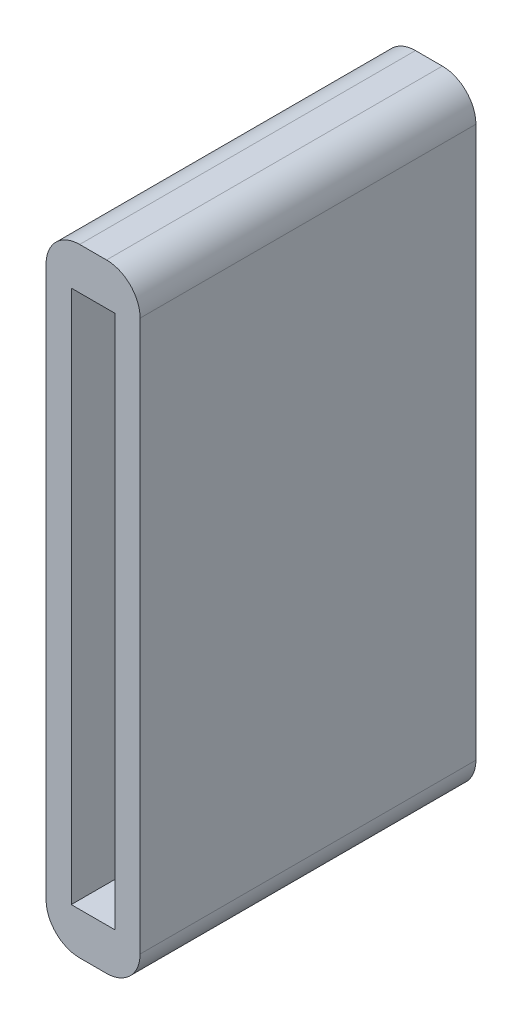
SolidWorks part; units mm, degrees
ref_plane "Plan de face" through (0, 0, 0) normal (0, 0, 1) x (1, 0, 0)
ref_plane "Plan de dessus" through (0, 0, 0) normal (0, 1, 0) x (1, 0, 0)
ref_plane "Plan de droite" through (0, 0, 0) normal (1, 0, 0) x (0, 0, -1)
sketch "Esquisse1" plane through (0, 0, 0) normal (0, 0, 1) x (1, 0, 0)
  line L0 (0.1886, 4.4615) -> (0.1886, -27.3385) construction
  line L1 (-1.1114, 4.4615) -> (1.4886, 4.4615)
  line L2 (-1.1114, 4.4615) -> (-1.1114, -27.3385)
  line L3 (-1.1114, -27.3385) -> (1.4886, -27.3385)
  line L4 (1.4886, 4.4615) -> (1.4886, -27.3385)
  line L5 (-2.6114, -29.8385) -> (2.9886, -29.8385)
  line L6 (-2.6114, -29.8385) -> (-2.6114, 6.9615)
  line L7 (-2.6114, 6.9615) -> (2.9886, 6.9615)
  line L8 (2.9886, -29.8385) -> (2.9886, 6.9615)
  line L9 (-1.1114, -11.4385) -> (1.4886, -11.4385) construction
  dimension "D1" = 2.6
  dimension "D2" = 31.8
  dimension "D3" = 2.5
  dimension "D4" = 1.5
extrude "Boss.-Extru.1" add sketch "Esquisse1" along normal blind 20
fillet "Congé1" radius 2 4 edges at (2.9886, 6.9615, 10) (2.9886, -29.8385, 10) (-2.6114, -29.8385, 10) (-2.6114, 6.9615, 10)
